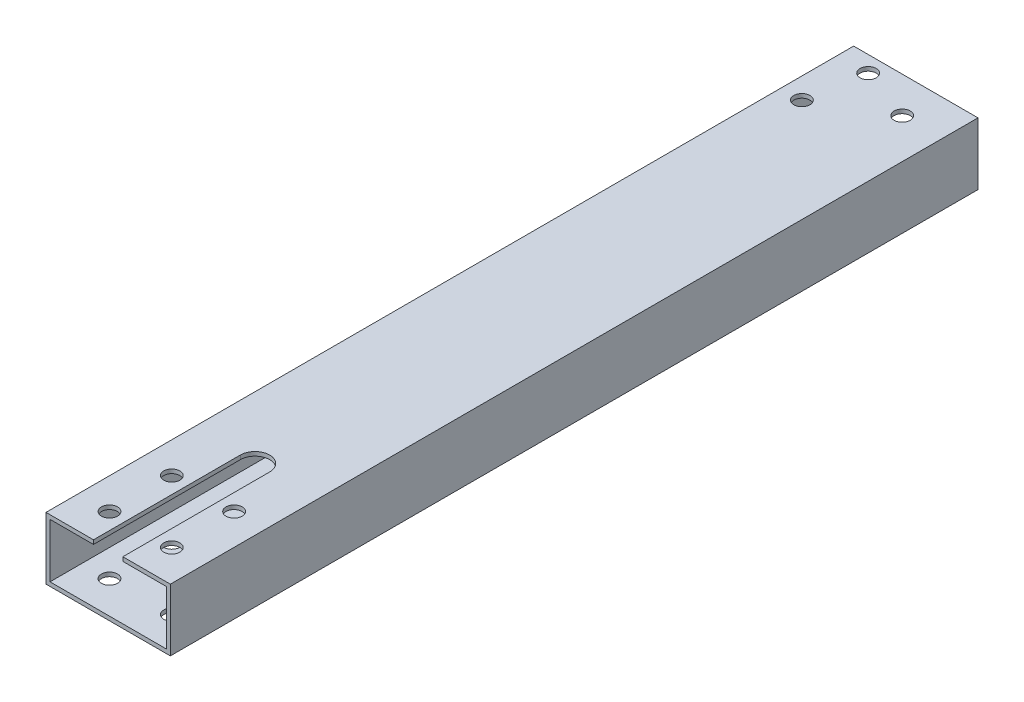
SolidWorks part; units mm, degrees
material "6061-O (SS)"
ref_plane "Front Plane" through (0, 0, 0) normal (0, 0, 1) x (1, 0, 0)
ref_plane "Top Plane" through (0, 0, 0) normal (0, 1, 0) x (1, 0, 0)
ref_plane "Right Plane" through (0, 0, 0) normal (1, 0, 0) x (0, 0, -1)
sketch "Sketch1" plane through (0, 0, 0) normal (0, 0, 1) x (1, 0, 0)
  line L1 (-25.4, 12.7) -> (25.4, 12.7)
  line L2 (-25.4, 12.7) -> (-25.4, -12.7)
  line L3 (-25.4, -12.7) -> (25.4, -12.7)
  line L4 (25.4, 12.7) -> (25.4, -12.7)
  line L5 (-23.749, 11.049) -> (23.749, 11.049)
  line L6 (-23.749, 11.049) -> (-23.749, -11.049)
  line L7 (-23.749, -11.049) -> (23.749, -11.049)
  line L8 (23.749, 11.049) -> (23.749, -11.049)
  point P8 (25.4, 0)
  point P10 (0, 12.7)
  dimension "D1" = 25.4
  dimension "D2" = 50.8
  dimension "D3" = 1.651
  dimension "D4" = 1.651
  dimension "D5" = 1.651
  dimension "D6" = 1.651
extrude "Boss-Extrude1" add sketch "Sketch1" along normal blind 330
sketch "Sketch2" plane through (0, 12.7, 0) normal (0, 1, 0) x (1, 0, 0)
  line L5 (-1.2369, -291.0676) -> (2.0631, -291.0676) construction
  line L8 (25.4, -330) -> (-25.4, -330) construction
  circle A2 centre (-1.2369, -291.0676) radius 3.3
  circle A3 centre (24.1785, -291.2923) radius 3.3
  circle A4 centre (23.9538, -316.7077) radius 3.3
  circle A5 centre (-1.4616, -316.483) radius 3.3
  circle A6 centre (11.4304, -304) radius 18 construction
  point P4 (0, 0)
  point P5 (0, 0)
  dimension "D2" = 26
  dimension "D5" = 4
sketch "Sketch4" plane through (0, 12.7, 0) normal (0, 1, 0) x (1, 0, 0)
  line L0 (-6, -270) -> (-6, -330)
  line L1 (6, -270) -> (6, -330)
  line L2 (-6, -330) -> (6, -330)
  line L5 (25.4, -330) -> (-25.4, -330) construction
  line L6 (25.4, -330) -> (25.4, 0) construction
  arc A0 (6, -270) -> (-6, -270) centre (0, -270) ccw
  point P21 (12.9594, -296.6096)
  dimension "D3" = 6
  dimension "D4" = 60
  dimension "D1" = 0
  dimension "D2" = 25.4
extrude "Cut-Extrude5" cut sketch "Sketch4" against normal up to next
sketch "Sketch8" plane through (0, 12.7, 0) normal (0, 1, 0) x (1, 0, 0)
  line L0 (0, -304) -> (20.6139, -324.6139)
  line L1 (0, -304) -> (-18.2537, -322.2537)
  line L2 (-21.5356, -304) -> (22.2859, -304)
  line L3 (25.4, -330) -> (6, -330) construction
  circle A0 centre (0, -304) radius 18 construction
  circle A3 centre (-12.7279, -316.7279) radius 3.3
  circle A4 centre (12.7279, -316.7279) radius 3.3
  circle A5 centre (12.7279, -291.2721) radius 3.3
  circle A6 centre (-12.7279, -291.2721) radius 3.3
  point P4 (0, 0)
  point P5 (0, 0)
  point P17 (0, -304)
  point P19 (0, 0)
  dimension "D1" = 36
  dimension "D2" = 6.6
  dimension "D3" = 4
  dimension "D6" = 26
  dimension "D4" = 90
  dimension "D5" = 45
extrude "Cut-Extrude6" cut sketch "Sketch8" against normal through all contours L1 A3 | L1 A3 | A6 | A5 | A4
hole_wizard "#00 Clearance Hole1" positions "Sketch10" profile "Sketch11" hole size "#00" standard "ANSI Inch" end condition through all
sketch "Sketch10" plane through (136.369, 20.7, -48.7158) normal (0, 1, 0) x (0.866, 0, -0.5)
  point P0 (-156.9016, 26.6954)
  point P1 (-141.9016, 8.6954)
  point P2 (-171.9016, 8.6954)
sketch "Sketch11" plane through (-12.8594, 20.7, 6.6161) normal (1, 0, 0) x (0, 0, 1)
  line L0 (0, 0) -> (0, 33.4)
  line L1 (0, 33.4) -> (3.3, 33.4)
  line L2 (3.3, 33.4) -> (3.3, 0)
  line L3 (3.3, 0) -> (0, 0)
  line L4 (0, -6.35) -> (0, 107.95) construction
  dimension "Thru Hole Dia." = 6.6
  dimension "Thru Hole Depth" = 33.4
